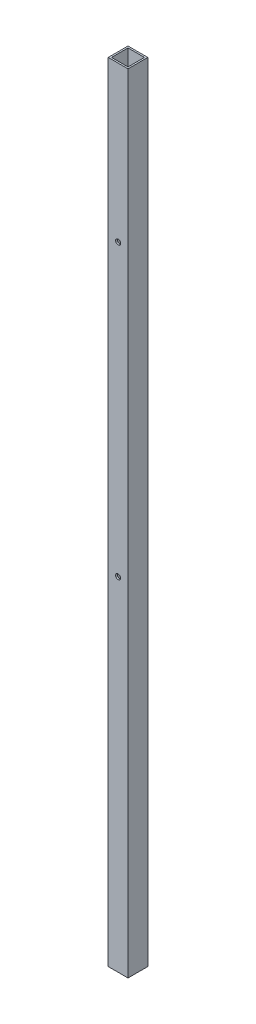
SolidWorks part; units mm, degrees
ref_plane "Front Plane" through (0, 0, 0) normal (0, 0, 1) x (1, 0, 0)
ref_plane "Top Plane" through (0, 0, 0) normal (0, 1, 0) x (1, 0, 0)
ref_plane "Right Plane" through (0, 0, 0) normal (1, 0, 0) x (0, 0, -1)
sketch "Sketch1" plane through (0, 0, 0) normal (0, 1, 0) x (0, 0, 1)
  line L1 (-9.525, 9.525) -> (9.525, 9.525)
  line L2 (-9.525, 9.525) -> (-9.525, -9.525)
  line L3 (-9.525, -9.525) -> (9.525, -9.525)
  line L4 (9.525, 9.525) -> (9.525, -9.525)
  line L5 (-9.525, 9.525) -> (9.525, -9.525) construction
  line L6 (-9.525, -9.525) -> (9.525, 9.525) construction
  line L7 (-7.9375, 7.9375) -> (7.9375, 7.9375)
  line L8 (-7.9375, 7.9375) -> (-7.9375, -7.9375)
  line L9 (-7.9375, -7.9375) -> (7.9375, -7.9375)
  line L10 (7.9375, 7.9375) -> (7.9375, -7.9375)
  line L11 (-7.9375, 7.9375) -> (7.9375, -7.9375) construction
  line L12 (-7.9375, -7.9375) -> (7.9375, 7.9375) construction
  point P0 (0, 0)
  point P5 (0, 0)
  dimension "D1" = 15.875
  dimension "D2" = 19.05
extrude "Boss-Extrude1" add sketch "Sketch1" along normal mid plane 758.9266
sketch "Sketch2" plane through (0, 0, 9.525) normal (0, 0, 1) x (1, 0, 0)
  line L0 (0, -379.4633) -> (0, -49.2633) construction
  line L1 (-9.525, -379.4633) -> (9.525, -379.4633) construction
  line L2 (0, -49.2633) -> (0, 230.1367) construction
  circle A0 centre (0, -49.2633) radius 2.4257
  circle A1 centre (0, 230.1367) radius 2.4257
  dimension "D1" = 4.8514
  dimension "D2" = 330.2
  dimension "D3" = 609.6
extrude "Shelf Holes" cut sketch "Sketch2" against normal up to next
sketch "Sketch3" plane through (0, 0, -9.525) normal (0, 0, -1) x (-1, 0, 0)
  line L0 (-9.525, 379.4633) -> (9.525, 379.4633) construction
  circle A0 centre (0, 112.3823) radius 4.7625
  circle A1 centre (0, -115.8621) radius 4.7625
  dimension "D1" = 9.525
  dimension "D2" = 267.081
  dimension "D3" = 228.2444
extrude "Cut-Extrude1" cut sketch "Sketch3" against normal up to next
equation "\"Height\"= 32in"
equation "\"Width\"= 23in"
equation "\"Depth\"= 20in"
equation "\"Plexi\"= .121in"
equation "\"MagnetThickness\"= 0.125in"
equation "\"MagnetDiameter\"= 12mm"
equation "\"DoorPlexi\" = \"Plexi\""
equation "\"BasePlateThickness\" = 0.5in"
equation "\"BasePlateWidth\" = \"Width\"+\"EBWidth\"-2*\"Plexi\""
equation "\"BasePlateDepth\" = \"TopBarDepth\"+2*\"CornerCube\""
equation "\"Boxsize\" = .75in"
equation "\"BoxsizeHalf\" = \"Boxsize\"/2"
equation "\"Boxinner\" = .625in"
equation "\"CornerCube\" = 0.75in"
equation "\"FingerLength\" = 1.125in"
equation "\"FingerWidth\" = .625in"
equation "\"Cutwidth\"= .016in"
equation "\"Earsize\"= 1in + \"Cutwidth\" /2"
equation "\"Slotsize\" = 1in - \"CutWidth\" / 2"
equation "\"InnerWidth\" = \"Width\" - 2* \"Plexi\""
equation "\"InnerHeight\" = \"Height\" -2 * \"Plexi\""
equation "\"InnerDepth\" = \"Depth\" - 2*\"Plexi\""
equation "\"RearNumHoles\" = 4"
equation "\"RearHolesBorder\" = 2.25"
equation "\"RearHoleSpacing\" = (\"Width\" - 2*\"RearHolesBorder\") / (\"RearNumHoles\"-1)"
equation "\"RearBarLength\" = (\"InnerWidth\"-2*\"CornerCube\")"
equation "\"RearTopNumHoles\" = 4"
equation "\"RearTopHolesBorder\" = 3.1"
equation "\"RearTopHolesSpacing\" = (\"Width\" - 2*\"RearTopHolesBorder\") / (\"RearTopNumHoles\"-1)"
equation "\"SideTopNumHoles\" = 4"
equation "\"SideTopHoleOffset\"=\"CornerCube\"+\"FingerLength\"+\"Plexi\"+.5"
equation "\"SideHorizNumHoles\" = 4"
equation "\"SideHorizHoleBorder\" = 1.50"
equation "\"SideVertBarLength\"=\"Height\"-\"BasePlateThickness\"-2*\"CornerCube\"-\"Plexi\""
equation "\"SideVertNumHoles\" = 4"
equation "\"SideVertHolesBorder\" = \"CornerCube\"+\"FingerLength\"+1.50"
equation "\"SideVertHoleSpacing\" = (\"InnerHeight\" - 2*\"SideVertHolesBorder\") / (\"SideVertNumHoles\"-1)"
equation "\"RearSideVertNumHoles\" = 4"
equation "\"RearSideVertHolesBorder\" = 2.4"
equation "\"RearSideVertHoleSpacing\" = (\"InnerHeight\" - 2*\"RearSideVertHolesBorder\") / (\"RearSideVertNumHoles\"-1)"
equation "\"RivetDia\" = .228in"
equation "\"SlotDepth\" = \"Plexi\" + 0.75in + .005in"
equation "\"SideSlotWidth\"   = \"Plexi\"+.005in"
equation "\"SidePanelVertSpacing\" = (\"Height\"-2*(1.75-\"Plexi\")) / 5"
equation "\"BottomPanelSideHoleSpacing\" = (\"InnerDepth\"-2*(1.75-\"Plexi\")) / 4"
equation "\"FrontDoorGap\" = .1in"
equation "\"TopDepth\" = \"Depth\"-\"DoorPlexi\"-\"FrontDoorGap\""
equation "\"TopBarDepth\" = \"Depth\"-\"DoorPlexi\"-\"Plexi\"-2*\"MagnetThickness\"-2*\"CornerCube\""
equation "\"CoolerDepth\" = 12in"
equation "\"ShelfDepth\" = \"TopBarDepth\"+\"CornerCube\"-\"CoolerDepth\""
equation "\"ShelfBarWidth\" = \"EBWidth\"-\"Boxsize\""
equation "\"ShelfGap\" = 0.5in"
equation "\"ShelfBarWidthShort\" = \"ShelfBarWidth\"-\"Boxsize\"-\"ShelfGap\""
equation "\"IntakeWidth\"=4in"
equation "\"IntakeHeight\"=2in"
equation "\"ExhaustWidth\"=4in"
equation "\"ExhaustHeight\"=2in"
equation "\"VentSpacing\"=7in"
equation "\"AngleBracketLength\"=20mm"
equation "\"AngleBracketWidth\"=.5in"
equation "\"AngleBracketThickness\"=.125in"
equation "\"AngleBracketHolePos\"=15mm"
equation "\"AngleBracketHoleDia\"=\"Rivet3_16Dia\""
equation "\"ShelfBarAngleHole\"=\"ShelfGap\"+\"Boxsize\"+\"AngleBracketHolePosShort\""
equation "\"D1@Boss-Extrude1\"=\"SideVertBarLength\""
equation "\"EBWidth\" = 9in"
equation "\"ComponentMountDia\"=0.1770"
equation "\"SideTopHoleSpacing\" = (\"TopBarDepth\"-2*\"SideTopHoleOffset\") / (\"SideTopNumHoles\"-1)"
equation "\"SideHorizHoleSpacing\" = (\"TopBarDepth\"-2*\"SideHorizHoleBorder\") / (\"SideHorizNumHoles\"-1)"
equation "\"ShelfBarDepth\"=\"ShelfDepth\"-2*\"CornerCube\""
equation "\"ShelfWidth\" = \"EBWidth\"-\"ShelfGap\""
equation "\"ShelfHeight1\" = 13in"
equation "\"ShelfHeight2\" = 24in"
equation "\"ShelfHeight3\"= 25in"
equation "\"VentVertLocation\"=12.75in"
equation "\"D2@Sketch2\"=\"ShelfHeight1\""
equation "\"D1@Sketch2\"=\"Rivet3_16Dia\""
equation "\"D3@Sketch2\"=\"ShelfHeight2\""
equation "\"ShelfThickness\" = .1250in"
equation "\"Rivet3_16Dia\" = .191in"
equation "\"BinderPostDia\" = .228in"
equation "\"PSBracketThickness\" = .0641in"
equation "\"EBForwardMountOffset\" = 4.0in"
equation "\"EBForwardMount\" = 2*\"Boxsize\"+\"CoolerDepth\"+\"EBForwardMountOffset\""
equation "\"EBRearwardMountOffset\" = 1.5in"
equation "\"EBRearwardMount\"= \"Boxsize\"+\"EBRearwardMountOffset\""
equation "\"AngleBracketLengthShort\"=.625in"
equation "\"AngleBracketLengthLong\"=1in"
equation "\"AngleBracketHolePosShort\"=.358in"
equation "\"AngleBracketHolePosLong\"=.7in"
equation "\"D2@Sketch3\"=\"RearSideVertHolesBorder\"-\"Plexi\"-\"CornerCube\"+\"RearSideVertHoleSpacing\""
equation "\"D3@Sketch3\"=\"RearSideVertHoleSpacing\""
